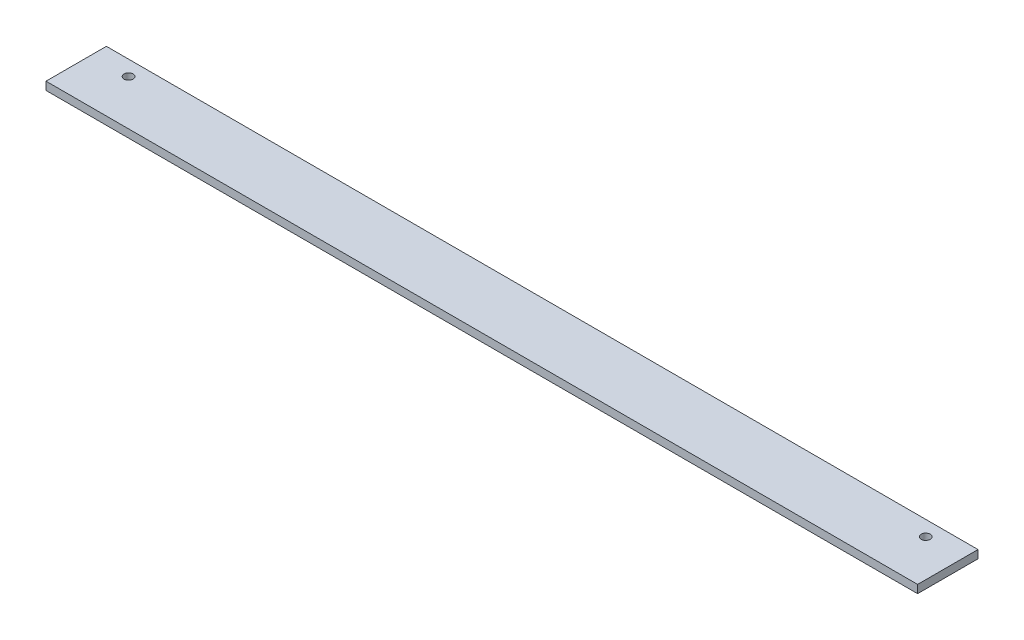
SolidWorks part; units mm, degrees
ref_plane "Спереди" through (0, 0, 0) normal (0, 0, 1) x (1, 0, 0)
ref_plane "Сверху" through (0, 0, 0) normal (0, 1, 0) x (1, 0, 0)
ref_plane "Справа" through (0, 0, 0) normal (1, 0, 0) x (0, 0, -1)
sketch "Эскиз1" plane through (0, 0, 0) normal (1, 0, 0) x (0, 0, -1)
  line L1 (-15, -2) -> (15, -2)
  line L2 (-15, -2) -> (-15, 2)
  line L3 (-15, 2) -> (15, 2)
  line L4 (15, -2) -> (15, 2)
  line L5 (-15, -2) -> (15, 2) construction
  line L6 (-15, 2) -> (15, -2) construction
  point P0 (0, 0)
  dimension "D1" = 4
  dimension "D2" = 30
extrude "Бобышка-Вытянуть1" add sketch "Эскиз1" along normal blind 433
sketch "Эскиз2" plane through (0, 2, 0) normal (0, 1, 0) x (1, 0, 0)
  line L0 (433, 15) -> (0, 15) construction
  line L1 (0, 15) -> (0, -15) construction
  line L2 (433, 15) -> (433, -15) construction
  circle A0 centre (18.5, 7.5) radius 2.25
  circle A1 centre (414.5, 7.5) radius 2.25
  dimension "D1" = 4.5
  dimension "D4" = 4.5
  dimension "D2" = 7.5
  dimension "D3" = 18.5
  dimension "D5" = 18.5
  dimension "D6" = 7.5
extrude "Вырез-Вытянуть1" cut sketch "Эскиз2" against normal through all
